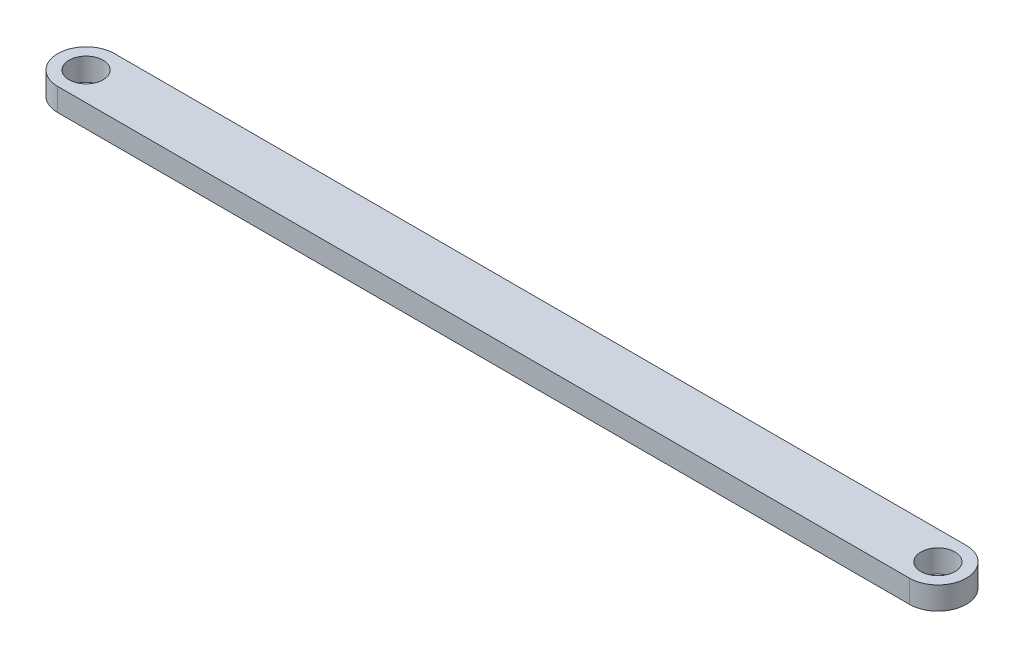
SolidWorks part; units mm, degrees
ref_plane "Front Plane" through (0, 0, 0) normal (0, 0, 1) x (1, 0, 0)
ref_plane "Top Plane" through (0, 0, 0) normal (0, 1, 0) x (1, 0, 0)
ref_plane "Right Plane" through (0, 0, 0) normal (1, 0, 0) x (0, 0, -1)
sketch "Sketch1" plane through (0, 0, 0) normal (0, 1, 0) x (1, 0, 0)
  line L0 (0, 0) -> (150, 0) construction
  line L1 (0, 5) -> (150, 5)
  line L2 (0, -5) -> (150, -5)
  line L3 (0, 5) -> (0, -5) construction
  circle A0 centre (0, 0) radius 3
  circle A1 centre (150, 0) radius 3
  circle A2 centre (0, 0) radius 5
  circle A3 centre (150, 0) radius 5
  dimension "D1" = 6
  dimension "D2" = 6
  dimension "D3" = 10
  dimension "D4" = 10
  dimension "D5" = 150
  dimension "D6" = 10
extrude "Boss-Extrude1" add sketch "Sketch1" along normal blind 4
